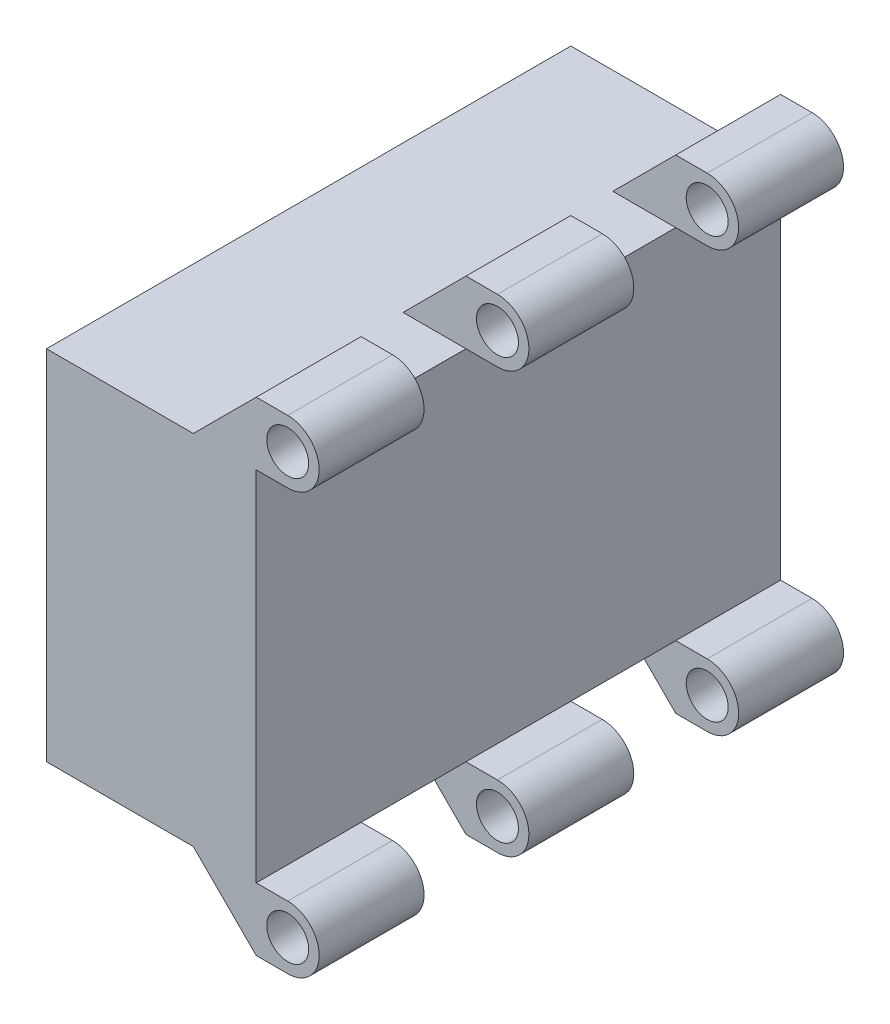
SolidWorks part; units mm, degrees
ref_plane "Front Plane" through (0, 0, 0) normal (0, 0, 1) x (1, 0, 0)
ref_plane "Top Plane" through (0, 0, 0) normal (0, 1, 0) x (1, 0, 0)
ref_plane "Right Plane" through (0, 0, 0) normal (1, 0, 0) x (0, 0, -1)
sketch "Sketch1" plane through (0, 0, 0) normal (1, 0, 0) x (0, 0, -1)
  line L1 (0, 0) -> (50, 0)
  line L2 (0, 0) -> (0, 34.11)
  line L3 (0, 34.11) -> (50, 34.11)
  line L4 (50, 0) -> (50, 34.11)
  dimension "D1" = 50
  dimension "D2" = 34.11
extrude "Boss-Extrude1" add sketch "Sketch1" along normal blind 20
sketch "Sketch2" plane through (0, 0, 0) normal (0, 0, 1) x (1, 0, 0)
  line L0 (20, 34.11) -> (0, 34.11) construction
  line L1 (20, 34.11) -> (20, 0) construction
  line L2 (20, 34.11) -> (23, 34.11)
  line L3 (23, 40.11) -> (20, 40.11)
  line L4 (23, 37.11) -> (23, 40.11) construction
  line L5 (23, 37.11) -> (23, 34.11) construction
  line L6 (20, 40.11) -> (14, 34.11)
  line L7 (14, 34.11) -> (20, 34.11)
  line L8 (20, 34.11) -> (40, 34.11) construction
  line L9 (21, 37.11) -> (20, 37.11) construction
  circle A0 centre (23, 37.11) radius 2
  arc A1 (23, 34.11) -> (23, 40.11) centre (23, 37.11) ccw
  dimension "D1" = 4
  dimension "D2" = 3
  dimension "D3" = 3
  dimension "D4" = 45
  dimension "D5" = 20
extrude "Boss-Extrude2" add sketch "Sketch2" against normal blind 10
pattern_linear "LPattern1" count 3 spacing 20 along (0, 0, -1) of "Boss-Extrude2"
ref_plane "Plane1" through (0, 17.055, 0) normal (0, 1, 0) x (1, 0, 0)
mirror "Mirror1" about plane through (0, 17.055, 0) normal (0, 1, 0) of "LPattern1", "Boss-Extrude2"
sketch "Sketch3" plane through (0, 0, 0) normal (-1, 0, 0) x (0, 0, 1)
  line L0 (-50, 17.055) -> (0, 17.055) construction
  line L1 (-50, 0) -> (-50, 34.11) construction
  line L2 (0, 34.11) -> (0, 0) construction
  line L3 (-37.5, 17.055) -> (-12.5, 17.055) construction
  line L4 (-37.5, 2.055) -> (-37.5, 32.055)
  line L5 (-37.5, 32.055) -> (-40.5, 32.055)
  line L6 (-37.5, 2.055) -> (-40.5, 2.055)
  line L7 (-40.5, 2.055) -> (-40.5, 32.055)
  line L8 (-25, 34.11) -> (-25, 0) construction
  line L9 (-30, 34.11) -> (-20, 34.11) construction
  line L10 (0, 0) -> (-50, 0) construction
  line L11 (-12.5, 2.055) -> (-9.5, 2.055)
  line L12 (-12.5, 2.055) -> (-12.5, 32.055)
  line L13 (-12.5, 32.055) -> (-9.5, 32.055)
  line L14 (-9.5, 2.055) -> (-9.5, 32.055)
  circle A0 centre (-25, 17.055) radius 8
  point P11 (-25, 17.055)
  point P14 (-37.5, 17.055)
  point P15 (-37.5, 17.055)
  dimension "D1" = 16
  dimension "D2" = 25
  dimension "D3" = 30
  dimension "D4" = 3
extrude "Cut-Extrude1" cut sketch "Sketch3" against normal blind 10
